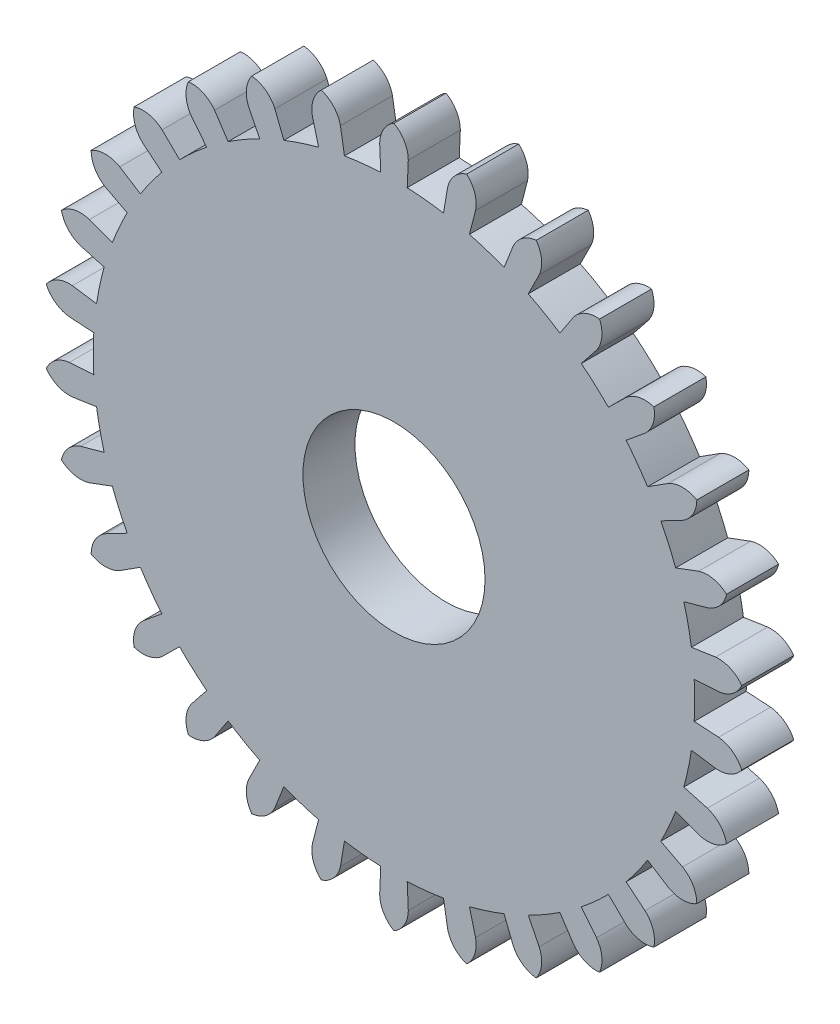
SolidWorks part; units mm, degrees
ref_plane "Front Plane" through (0, 0, 0) normal (0, 0, 1) x (1, 0, 0)
ref_plane "Top Plane" through (0, 0, 0) normal (0, 1, 0) x (1, 0, 0)
ref_plane "Right Plane" through (0, 0, 0) normal (1, 0, 0) x (0, 0, -1)
sketch "Sketch1" plane through (0, 0, 0) normal (0, 0, 1) x (1, 0, 0)
  line L0 (-0.55, 0) -> (0.55, 0) construction
  line L1 (-0.55, 0) -> (0.55, 0) construction
  line L2 (0, 13.4405) -> (0, 12.5) construction
  line L3 (-0.55, 12.4879) -> (-0.5086, 11.5483)
  line L6 (0.55, 12.4879) -> (0.5086, 11.5483)
  circle A0 centre (0, 0) radius 12.5 construction
  circle A1 centre (0, 0) radius 3.5 construction
  circle A2 centre (0, 0) radius 12.5 construction
  circle A3 centre (0, 0) radius 3.5
  arc A4 (-0.5086, 11.5483) -> (0.5086, 11.5483) centre (0, 0) ccw
  arc A5 (0, 13.4405) -> (-0.55, 12.4879) centre (0.55, 12.4879) ccw
  arc A6 (0.55, 12.4879) -> (0, 13.4405) centre (-0.55, 12.4879) ccw
extrude "Boss-Extrude1" add sketch "Sketch1" against normal up to vertex (2 mm away)
pattern_circular "CirPattern1" count 30 over 360 about axis through (0, 0, 0) along (0, 0, 1) of "Boss-Extrude1"
equation "\"teeth\"= 30"
equation "\"D1@CirPattern1\"=\"teeth\""
